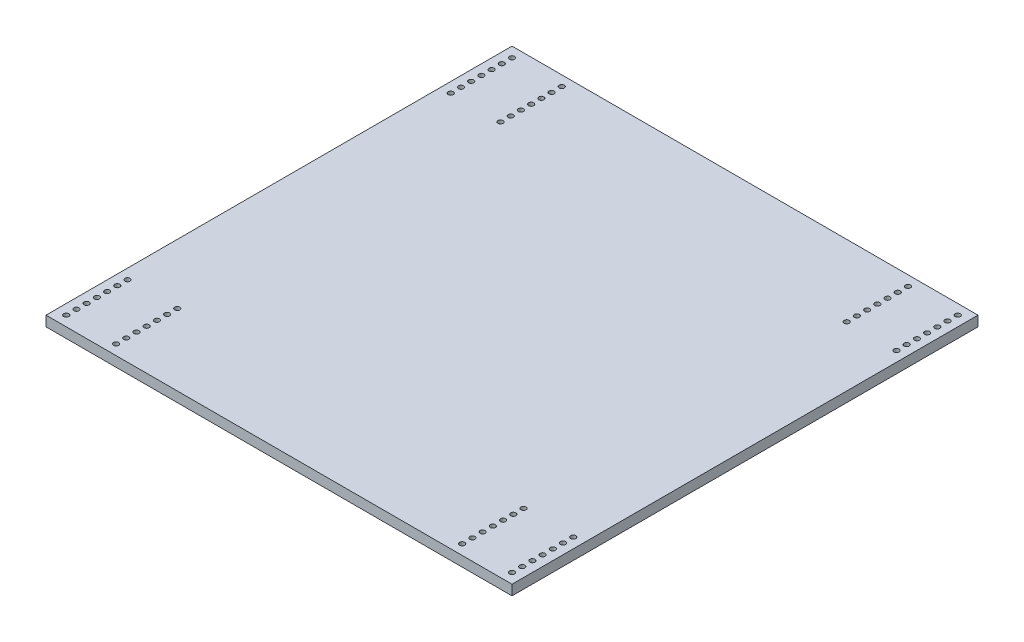
SolidWorks part; units mm, degrees
material "Acrylic (Medium-high impact)"
ref_plane "Front Plane" through (0, 0, 0) normal (0, 0, 1) x (1, 0, 0)
ref_plane "Top Plane" through (0, 0, 0) normal (0, 1, 0) x (1, 0, 0)
ref_plane "Right Plane" through (0, 0, 0) normal (1, 0, 0) x (0, 0, -1)
sketch "Sketch1" plane through (0, 0, 0) normal (0, 1, 0) x (1, 0, 0)
  line L1 (-146.05, -146.05) -> (146.05, -146.05)
  line L2 (-146.05, -146.05) -> (-146.05, 146.05)
  line L3 (-146.05, 146.05) -> (146.05, 146.05)
  line L4 (146.05, -146.05) -> (146.05, 146.05)
  line L5 (-146.05, -146.05) -> (146.05, 146.05) construction
  line L6 (-146.05, 146.05) -> (146.05, -146.05) construction
  point P0 (0, 0)
  dimension "D1" = 292.1
  dimension "D2" = 292.1
extrude "Boss-Extrude1" add sketch "Sketch1" along normal blind 6.35
sketch "Sketch2" plane through (0, 6.35, 0) normal (0, 1, 0) x (1, 0, 0)
  line L0 (-139.7, -146.05) -> (-139.7, 146.05) construction
  line L1 (-146.05, -146.05) -> (146.05, -146.05) construction
  line L2 (-146.05, 146.05) -> (-146.05, -146.05) construction
  line L3 (146.05, 146.05) -> (-146.05, 146.05) construction
  line L4 (0, 146.05) -> (0, -146.05) construction
  line L5 (-146.05, 0) -> (146.05, 0) construction
  line L6 (146.05, -146.05) -> (146.05, 146.05) construction
  line L7 (-124.1, 146.05) -> (-124.1, -146.05) construction
  line L8 (-108.5, -146.05) -> (-108.5, 146.05) construction
  line L9 (108.5, -146.05) -> (108.5, 146.05) construction
  line L10 (124.1, 146.05) -> (124.1, -146.05) construction
  line L11 (139.7, -146.05) -> (139.7, 146.05) construction
  circle A0 centre (-139.7, -139.7) radius 1.6
  circle A1 centre (-139.7, -133.3) radius 1.6
  circle A2 centre (-139.7, -126.9) radius 1.6
  circle A3 centre (-139.7, -120.5) radius 1.6
  circle A4 centre (-139.7, -114.1) radius 1.6
  circle A5 centre (-139.7, -107.7) radius 1.6
  circle A6 centre (-139.7, -101.3) radius 1.6
  circle A7 centre (-139.7, 101.3) radius 1.6
  circle A8 centre (-139.7, 107.7) radius 1.6
  circle A9 centre (-139.7, 114.1) radius 1.6
  circle A10 centre (-139.7, 120.5) radius 1.6
  circle A11 centre (-139.7, 126.9) radius 1.6
  circle A12 centre (-139.7, 133.3) radius 1.6
  circle A13 centre (-139.7, 139.7) radius 1.6
  circle A14 centre (-108.5, 139.7) radius 1.6
  circle A15 centre (-108.5, 133.3) radius 1.6
  circle A16 centre (-108.5, 126.9) radius 1.6
  circle A17 centre (-108.5, 120.5) radius 1.6
  circle A18 centre (-108.5, 114.1) radius 1.6
  circle A19 centre (-108.5, 107.7) radius 1.6
  circle A20 centre (-108.5, 101.3) radius 1.6
  circle A21 centre (-108.5, -101.3) radius 1.6
  circle A22 centre (-108.5, -107.7) radius 1.6
  circle A23 centre (-108.5, -114.1) radius 1.6
  circle A24 centre (-108.5, -120.5) radius 1.6
  circle A25 centre (-108.5, -126.9) radius 1.6
  circle A26 centre (-108.5, -133.3) radius 1.6
  circle A27 centre (-108.5, -139.7) radius 1.6
  circle A28 centre (108.5, -139.7) radius 1.6
  circle A29 centre (108.5, -133.3) radius 1.6
  circle A30 centre (108.5, -126.9) radius 1.6
  circle A31 centre (108.5, -120.5) radius 1.6
  circle A32 centre (108.5, -114.1) radius 1.6
  circle A33 centre (108.5, -107.7) radius 1.6
  circle A34 centre (108.5, -101.3) radius 1.6
  circle A35 centre (108.5, 101.3) radius 1.6
  circle A36 centre (108.5, 107.7) radius 1.6
  circle A37 centre (108.5, 114.1) radius 1.6
  circle A38 centre (108.5, 120.5) radius 1.6
  circle A39 centre (108.5, 126.9) radius 1.6
  circle A40 centre (108.5, 133.3) radius 1.6
  circle A41 centre (108.5, 139.7) radius 1.6
  circle A42 centre (139.7, 139.7) radius 1.6
  circle A43 centre (139.7, 133.3) radius 1.6
  circle A44 centre (139.7, 126.9) radius 1.6
  circle A45 centre (139.7, 120.5) radius 1.6
  circle A46 centre (139.7, 114.1) radius 1.6
  circle A47 centre (139.7, 107.7) radius 1.6
  circle A48 centre (139.7, 101.3) radius 1.6
  circle A49 centre (139.7, -101.3) radius 1.6
  circle A50 centre (139.7, -107.7) radius 1.6
  circle A51 centre (139.7, -114.1) radius 1.6
  circle A52 centre (139.7, -120.5) radius 1.6
  circle A53 centre (139.7, -126.9) radius 1.6
  circle A54 centre (139.7, -133.3) radius 1.6
  circle A55 centre (139.7, -139.7) radius 1.6
  point P136 (0, 0)
  dimension "D2" = 3.2
  dimension "D1" = 6.35
  dimension "D3" = 6.35
  dimension "D5" = 15.6
  dimension "D6" = 6.4
  dimension "D4" = 7
extrude "Cut-Extrude2" cut sketch "Sketch2" against normal through all
